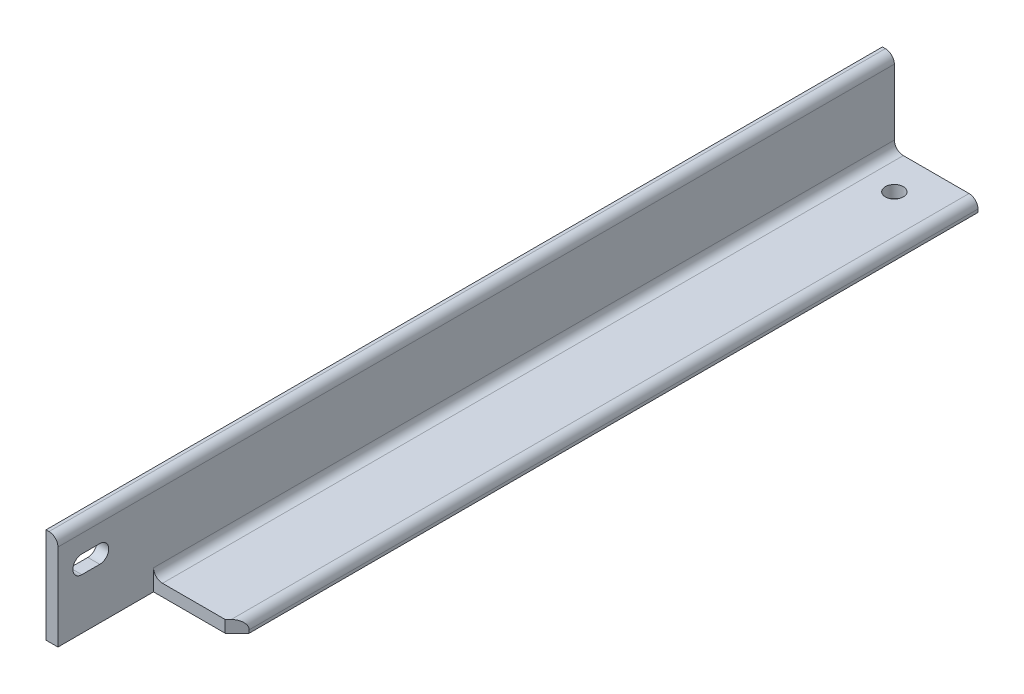
SolidWorks part; units mm, degrees
ref_plane "Front Plane" through (0, 0, 0) normal (0, 0, 1) x (1, 0, 0)
ref_plane "Top Plane" through (0, 0, 0) normal (0, 1, 0) x (1, 0, 0)
ref_plane "Right Plane" through (0, 0, 0) normal (1, 0, 0) x (0, 0, -1)
sketch "Sketch1" plane through (0, 0, 0) normal (0, 0, 1) x (1, 0, 0)
  line L0 (0, 0) -> (0, 101.6)
  line L1 (0, 101.6) -> (3.1801, 101.6)
  line L2 (12.7, 92.0801) -> (12.7, 22.225)
  line L3 (22.225, 12.7) -> (92.0801, 12.7)
  line L4 (101.6, 3.1801) -> (101.6, 0)
  line L5 (101.6, 0) -> (0, 0)
  arc A0 (101.6, 3.1801) -> (92.0801, 12.7) centre (92.0801, 3.1801) ccw
  arc A1 (3.1801, 101.6) -> (12.7, 92.0801) centre (3.1801, 92.0801) cw
  arc A2 (22.225, 12.7) -> (12.7, 22.225) centre (22.225, 22.225) cw
  circle A3 centre (0, 0) radius 9.525 construction
  dimension "D2" = 3.1801
  dimension "Radius_1" = 9.525
  dimension "Radius_2" = 9.525
  dimension "D1" = 12.7
  dimension "V_leg" = 101.6
  dimension "H_leg" = 101.6
  dimension "Thickness" = 12.7
  dimension "Flat_wid" = 3.1801
extrude "Boss-Extrude1" add sketch "Sketch1" along normal mid plane 889
sketch "Sketch2" plane through (0, 0, 0) normal (0, -1, 0) x (1, 0, 0)
  line L0 (88.9, 342.9) -> (12.7, 342.9)
  line L1 (101.6, 444.5) -> (101.6, -444.5) construction
  line L2 (12.7, 495.3) -> (101.6, 342.9) construction
  line L3 (12.7, 342.9) -> (12.7, 444.5)
  line L4 (12.7, 444.5) -> (101.6, 444.5)
  line L5 (101.6, 444.5) -> (101.6, 342.9)
  line L6 (0, 444.5) -> (0, -444.5) construction
  line L9 (88.9, 342.9) -> (101.6, 330.2)
  line L10 (101.6, 342.9) -> (101.6, 330.2)
  dimension "D1" = 12.7
  dimension "D2" = 88.9
  dimension "D3" = 101.6
  dimension "D4" = 12.7
  dimension "D5" = 101.6
  dimension "D6" = 12.7
extrude "Cut-Extrude1" cut sketch "Sketch2" against normal up to next
sketch "Sketch3" plane through (0, 0, 0) normal (-1, 0, 0) x (0, 0, 1)
  line L0 (419.1, 63.5) -> (400.05, 63.5) construction
  line L1 (419.1, 53.975) -> (400.05, 53.975)
  line L2 (419.1, 73.025) -> (400.05, 73.025)
  line L3 (444.5, 0) -> (-444.5, 0) construction
  line L4 (444.5, 101.6) -> (444.5, 0) construction
  arc A0 (419.1, 53.975) -> (419.1, 73.025) centre (419.1, 63.5) ccw
  arc A1 (400.05, 73.025) -> (400.05, 53.975) centre (400.05, 63.5) ccw
  point P2 (409.575, 63.5)
  dimension "D1" = 9.525
  dimension "D2" = 63.5
  dimension "D3" = 19.05
  dimension "D4" = 25.4
extrude "Cut-Extrude2" cut sketch "Sketch3" against normal up to next
hole_wizard "3/4 (0.75) Diameter Hole1" positions "Sketch5" profile "Sketch4" hole size "3/4" standard "Ansi Inch"
sketch "Sketch5" plane through (0, 0, 0) normal (0, -1, 0) x (1, 0, 0)
  line L0 (0, 444.5) -> (0, -444.5) construction
  line L1 (0, -444.5) -> (101.6, -444.5) construction
  point P0 (50.8, -406.4)
  dimension "D1" = 50.8
  dimension "D2" = 38.1
sketch "Sketch4" plane through (50.8, 0, -406.4) normal (1, 0, 0) x (0, 0, -1)
  line L0 (0, 0) -> (0, 56.5232)
  line L1 (0, 56.5232) -> (9.525, 50.8)
  line L2 (9.525, 50.8) -> (9.525, 0)
  line L5 (9.525, 0) -> (0, 0)
  line L10 (0, 56.5232) -> (-9.525, 50.8) construction
  line L11 (0, -6.35) -> (0, 107.95) construction
  dimension "Hole Dia." = 19.05
  dimension "Hole Depth" = 50.8
  dimension "Drill Angle" = 118
